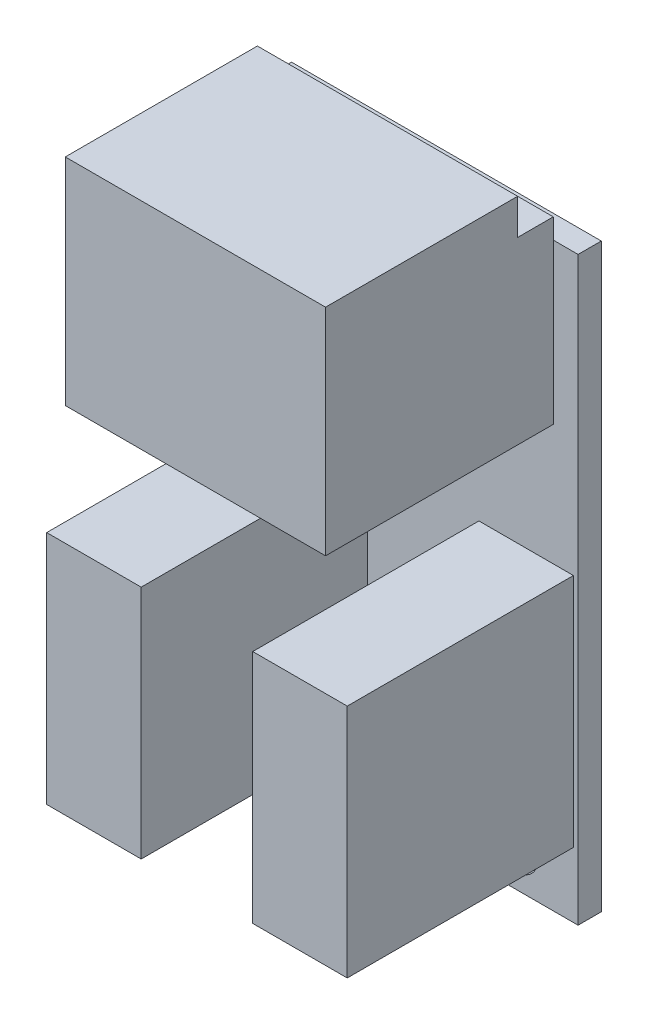
SolidWorks part; units mm, degrees
ref_plane "Alzado" through (0, 0, 0) normal (0, 0, 1) x (1, 0, 0)
ref_plane "Planta" through (0, 0, 0) normal (0, 1, 0) x (1, 0, 0)
ref_plane "Vista lateral" through (0, 0, 0) normal (1, 0, 0) x (0, 0, -1)
sketch "Croquis1" plane through (0, 0, 0) normal (0, 0, 1) x (1, 0, 0)
  line L0 (-10, -16.4) -> (-6.05, -16.4) construction
  line L1 (10, -18.75) -> (-10, -18.75)
  line L2 (10, -18.75) -> (10, 18.75)
  line L3 (10, 18.75) -> (-10, 18.75)
  line L4 (-10, -18.75) -> (-10, 18.75)
  line L5 (10, -18.75) -> (-10, 18.75) construction
  line L6 (10, 18.75) -> (-10, -18.75) construction
  line L7 (-6.05, -16.4) -> (6.05, -16.4) construction
  line L8 (6.05, -16.4) -> (10, -16.4) construction
  line L9 (6.05, -17.75) -> (6.05, -18.75) construction
  circle A0 centre (-6.05, -16.4) radius 1.35
  circle A1 centre (6.05, -16.4) radius 1.35
  point P0 (0, 0)
  point P14 (-4.7, -16.4)
  point P15 (4.7, -16.4)
  dimension "D3" = 2.7
  dimension "D1" = 37.5
  dimension "D2" = 20
  dimension "D4" = 1
  dimension "D5" = 9.4
extrude "Saliente-Extruir1" add sketch "Croquis1" along normal blind 1.5
sketch "Croquis2" plane through (0, 0, 1.5) normal (0, 0, 1) x (1, 0, 0)
  line L0 (8.4, 8.45) -> (8.4, 20.05)
  line L1 (8.4, 8.45) -> (-8.4, 8.45)
  line L2 (8.4, 20.05) -> (-8.4, 20.05)
  line L3 (-8.4, 8.45) -> (-8.4, 20.05)
  line L4 (8.4, 8.45) -> (-8.4, 20.05) construction
  line L5 (8.4, 20.05) -> (-8.4, 8.45) construction
  line L6 (10, 18.75) -> (-10, 18.75) construction
  line L7 (0, 14.25) -> (0, 0) construction
  point P1 (0, 14.25)
  dimension "D1" = 1.3
  dimension "D2" = 16.8
  dimension "D3" = 11.6
extrude "Saliente-Extruir2" add sketch "Croquis2" along normal blind 2.3
sketch "Croquis3" plane through (0, 0, 3.8) normal (0, 0, 1) x (1, 0, 0)
  line L0 (8.4, 8.45) -> (8.4, 20.05) construction
  line L1 (-8.4, 8.45) -> (8.4, 8.45)
  line L2 (-8.4, 8.45) -> (-8.4, 22.35)
  line L3 (-8.4, 22.35) -> (8.4, 22.35)
  line L4 (8.4, 8.45) -> (8.4, 22.35)
  dimension "D1" = 13.9
extrude "Saliente-Extruir3" add sketch "Croquis3" along normal blind 12.4
sketch "Croquis4" plane through (0, 0, 1.5) normal (0, 0, 1) x (1, 0, 0)
  line L1 (-9.7, 0.65) -> (-3.6, 0.65)
  line L2 (-9.7, 0.65) -> (-9.7, -14.55)
  line L3 (-9.7, -14.55) -> (-3.6, -14.55)
  line L4 (-3.6, 0.65) -> (-3.6, -14.55)
  line L6 (9.7, 0.65) -> (3.6, 0.65)
  line L7 (9.7, 0.65) -> (9.7, -14.55)
  line L8 (9.7, -14.55) -> (3.6, -14.55)
  line L9 (3.6, 0.65) -> (3.6, -14.55)
  line L10 (-8.4, 8.45) -> (8.4, 8.45) construction
  line L11 (-10, 18.75) -> (-10, -18.75) construction
  line L12 (10, -18.75) -> (10, 18.75) construction
  dimension "D1" = 7.8
  dimension "D2" = 15.2
  dimension "D3" = 6.1
  dimension "D4" = 0.3
  dimension "D5" = 0.3
extrude "Saliente-Extruir4" add sketch "Croquis4" along normal blind 14.6
